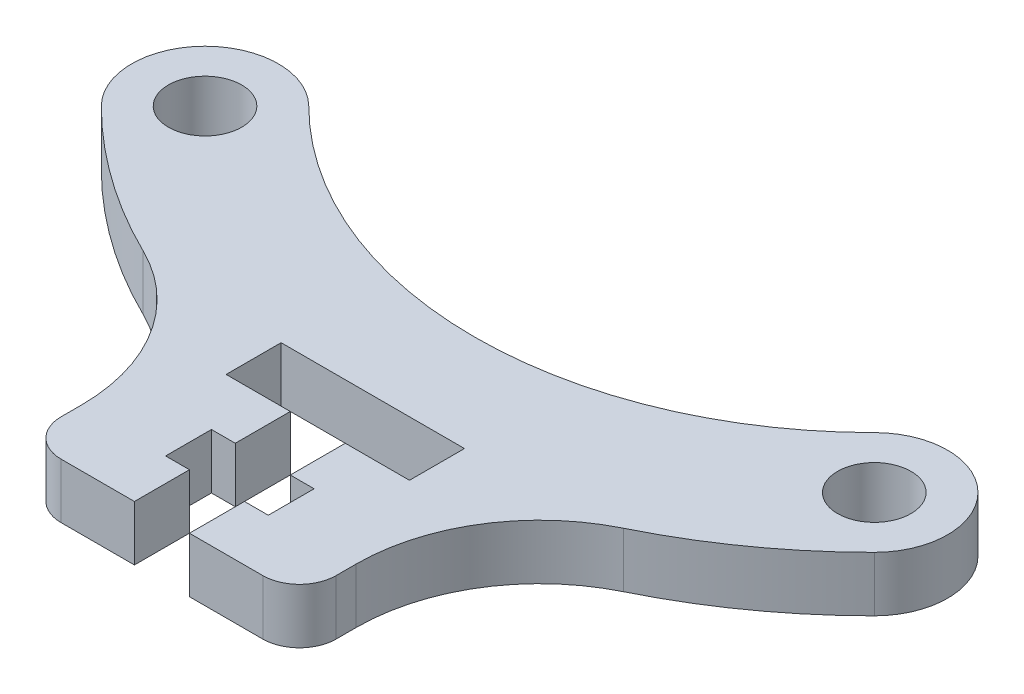
SolidWorks part; units mm, degrees
ref_plane "Front Plane" through (0, 0, 0) normal (0, 0, 1) x (1, 0, 0)
ref_plane "Top Plane" through (0, 0, 0) normal (0, 1, 0) x (1, 0, 0)
ref_plane "Right Plane" through (0, 0, 0) normal (1, 0, 0) x (0, 0, -1)
sketch "Sketch1" plane through (0, 0, 0) normal (0, 1, 0) x (1, 0, 0)
  line L0 (-18.25, 0) -> (18.25, 0) construction
  line L1 (0, 18.2509) -> (18.25, 0) construction
  line L2 (18.25, 0) -> (21.0784, -2.8285) construction
  line L3 (21.0784, -2.8285) -> (-21.0784, -2.8285) construction
  line L4 (-21.0784, -2.8285) -> (-18.25, 0) construction
  line L5 (-18.25, 0) -> (0, 18.2509) construction
  circle A0 centre (-18.25, 0) radius 2
  circle A1 centre (18.25, 0) radius 2
  circle A2 centre (0, 18.2509) radius 25.81 construction
  arc A3 (-21.0784, -2.8285) -> (21.0784, -2.8285) centre (0, 18.2509) ccw
  arc A4 (-15.4216, 2.8285) -> (15.4216, 2.8285) centre (0, 18.2509) ccw
  arc A5 (-15.4216, 2.8285) -> (-21.0784, -2.8285) centre (-18.25, 0) ccw
  arc A6 (15.4216, 2.8285) -> (21.0784, -2.8285) centre (18.25, 0) cw
  point P4 (0, 0)
  dimension "D2" = 4
  dimension "D3" = 51.62
  dimension "D5" = 4
  dimension "D1" = 36.5
  dimension "D4" = 4
extrude "Boss-Extrude1" add sketch "Sketch1" along normal blind 3 contours A6 A4 A5 A3 A1 A0
sketch "Sketch2" plane through (0, 3, 0) normal (0, 1, 0) x (1, 0, 0)
  line L0 (-7.5, -10.6003) -> (-7.5, -20.6003)
  line L1 (-7.5, -20.6003) -> (7.5, -20.6003)
  line L2 (7.5, -20.6003) -> (7.5, -10.6003)
  line L5 (0, 18.2509) -> (0, -20.6003) construction
  arc A0 (-21.0784, -2.8285) -> (21.0784, -2.8285) centre (0, 18.2509) ccw construction
  arc A1 (-7.5, -10.6003) -> (7.5, -10.6003) centre (0, 18.2509) ccw
  point P8 (2.0793, -11.4865)
  dimension "D3" = 10
  dimension "D1" = 15
extrude "Boss-Extrude2" add sketch "Sketch2" against normal blind 3
sketch "Sketch4" plane through (0, 3, 0) normal (0, 1, 0) x (1, 0, 0)
  line L0 (-1.5, -20.6003) -> (-1.5, -17.6003)
  line L1 (-7.5, -20.6003) -> (7.5, -20.6003) construction
  line L2 (-1.5, -17.6003) -> (-2.8, -17.6003)
  line L3 (-2.8, -17.6003) -> (-2.8, -15.1003)
  line L4 (-2.8, -15.1003) -> (-1.5, -15.1003)
  line L5 (-1.5, -15.1003) -> (-1.5, -12.1003)
  line L6 (-1.5, -12.1003) -> (-5, -12.1003)
  line L7 (-5, -12.1003) -> (-5, -9.1003)
  line L8 (-5, -9.1003) -> (5, -9.1003)
  line L9 (5, -9.1003) -> (5, -12.1003)
  line L10 (5, -12.1003) -> (1.5, -12.1003)
  line L11 (1.5, -12.1003) -> (1.5, -15.1003)
  line L12 (1.5, -15.1003) -> (2.8, -15.1003)
  line L13 (2.8, -15.1003) -> (2.8, -17.6003)
  line L14 (2.8, -17.6003) -> (1.5, -17.6003)
  line L15 (1.5, -17.6003) -> (1.5, -20.6003)
  line L16 (-1.5, -20.6003) -> (1.5, -20.6003)
  line L17 (-1.5, -12.1003) -> (0, -12.1003) construction
  line L18 (0, -9.1003) -> (0, -20.6003) construction
  line L19 (0, -12.1003) -> (1.5, -12.1003) construction
  point P18 (1.5, -13.6003)
  point P19 (0, -20.6003)
  dimension "D1" = 3
  dimension "D2" = 5.6
  dimension "D3" = 3
  dimension "D4" = 2.5
  dimension "D5" = 3
  dimension "D6" = 10
  dimension "D7" = 3
extrude "Cut-Extrude2" cut sketch "Sketch4" against normal blind 3
fillet "Fillet1" radius 10 2 edges at (7.5, 1.5, 10.6003) (-7.5, 1.5, 10.6003)
fillet "Fillet2" radius 2 2 edges at (7.5, 1.5, 20.6003) (-7.5, 1.5, 20.6003)
